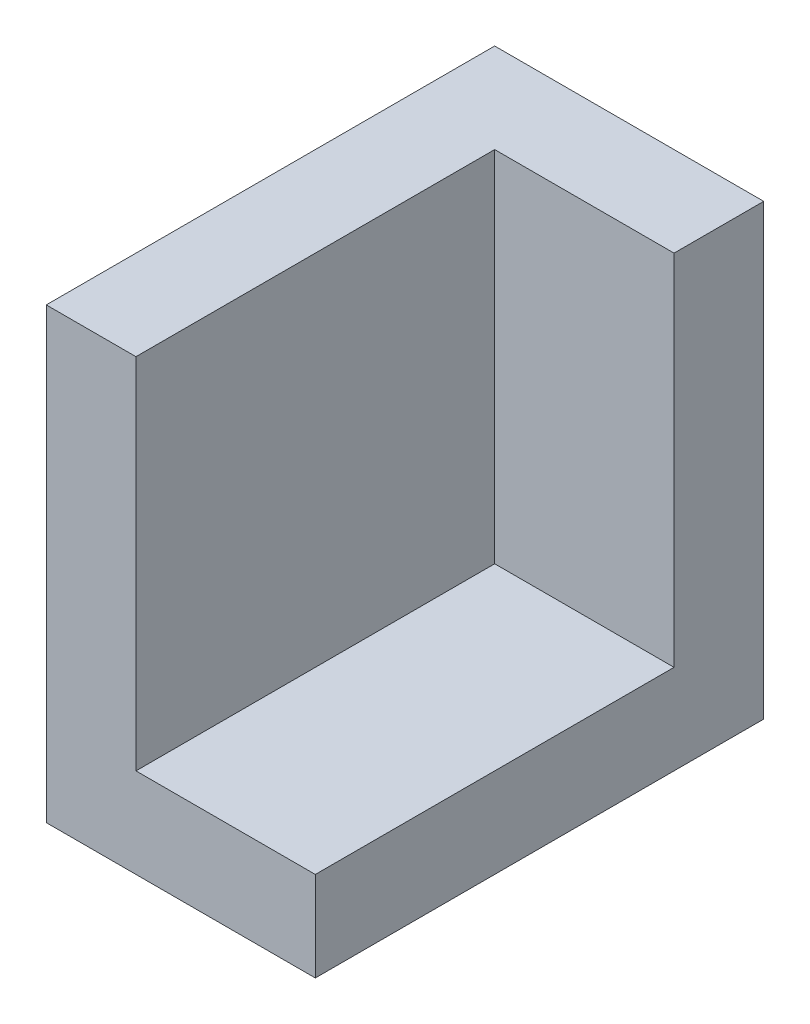
SolidWorks part; units mm, degrees
ref_plane "Front Plane" through (0, 0, 0) normal (0, 0, 1) x (1, 0, 0)
ref_plane "Top Plane" through (0, 0, 0) normal (0, 1, 0) x (1, 0, 0)
ref_plane "Right Plane" through (0, 0, 0) normal (1, 0, 0) x (0, 0, -1)
sketch "Sketch1" plane through (0, 0, 0) normal (1, 0, 0) x (0, 0, -1)
  line L0 (0, 0) -> (0, 20)
  line L1 (0, 20) -> (5, 20)
  line L2 (5, 20) -> (5, -5)
  line L3 (5, -5) -> (-20, -5)
  line L4 (-20, -5) -> (-20, 0)
  line L5 (-20, 0) -> (0, 0)
  dimension "D1" = 5
  dimension "D2" = 5
  dimension "D3" = 20
  dimension "D4" = 20
extrude "Boss-Extrude1" add sketch "Sketch1" along normal blind 10
sketch "Sketch2" plane through (0, 0, 0) normal (1, 0, 0) x (0, 0, -1)
  line L0 (-20, -5) -> (5, -5) construction
  line L1 (5, -5) -> (5, 20) construction
  line L2 (-20, -5) -> (5, -5)
  line L3 (5, -5) -> (5, 20)
  line L4 (5, 20) -> (-20, 20)
  line L5 (-20, 20) -> (-20, -5)
extrude "Boss-Extrude2" add sketch "Sketch2" against normal blind 5
